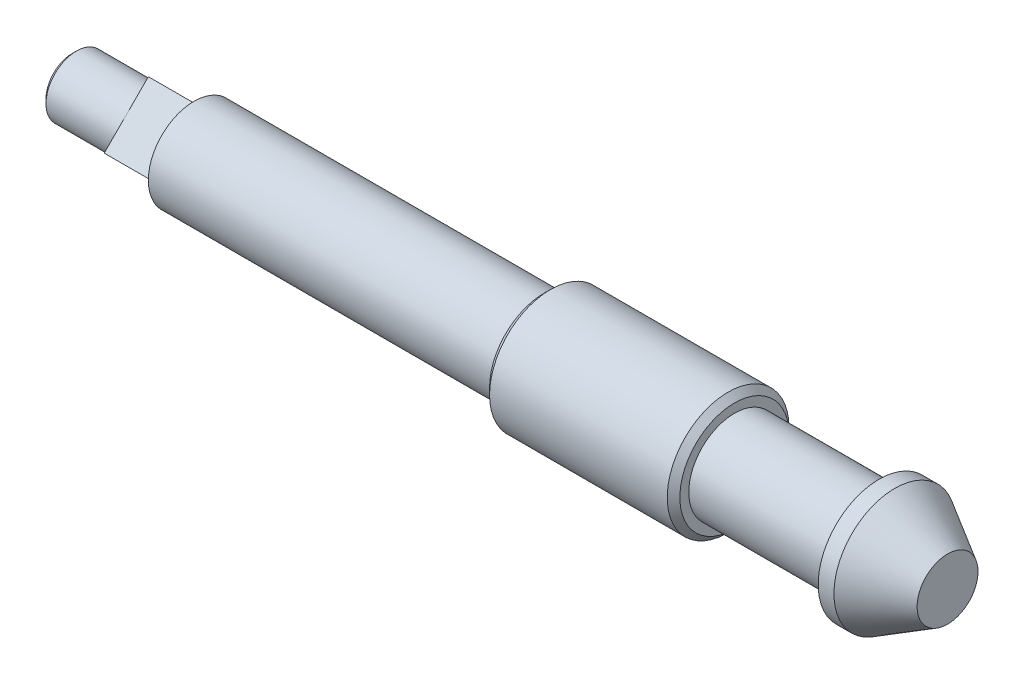
SolidWorks part; units mm, degrees
material "Сталь"
ref_plane "Спереди" through (0, 0, 0) normal (0, 0, 1) x (1, 0, 0)
ref_plane "Сверху" through (0, 0, 0) normal (0, 1, 0) x (1, 0, 0)
ref_plane "Справа" through (0, 0, 0) normal (1, 0, 0) x (0, 0, -1)
sketch "Эскиз1" plane through (0, 0, 0) normal (0, 0, 1) x (1, 0, 0)
  line L0 (0, 0) -> (-155.4845, 0) construction
  line L1 (0, 0) -> (0, 4)
  line L2 (0, 4) -> (-6.9282, 8)
  line L3 (-6.9282, 8) -> (-9, 8)
  line L4 (-9, 8) -> (-9, 6)
  line L5 (-9, 6) -> (-28, 6)
  line L6 (-28, 6) -> (-28, 8)
  line L7 (-28, 8) -> (-53, 8)
  line L8 (-53, 8) -> (-53, 6)
  line L9 (-53, 6) -> (-115, 6)
  line L10 (-115, 6) -> (-115, 0)
  line L11 (0, 0) -> (-115, 0)
  dimension "D1" = 115
  dimension "D2" = 9
  dimension "D3" = 8
  dimension "D4" = 60
  dimension "D5" = 4
  dimension "D6" = 12
  dimension "D7" = 16
  dimension "D8" = 25
  dimension "D9" = 28
revolve "Повернуть1" add sketch "Эскиз1" angle 360 about L0
cosmetic thread "Условное изображение резьбы1" parameters "D1"=5, "D2"=14.344
chamfer "Фаска1" distance 0.828 angle 45 2 edges at (-53, 0, -8) (-28, 0, -8)
sketch "Эскиз2" plane through (-115, 0, 0) normal (-1, 0, 0) x (0, 0, 1)
  circle A0 centre (0, 0) radius 4
  circle A1 centre (0, 0) radius 6 construction
  circle A2 centre (0, 0) radius 6
  dimension "D1" = 8
extrude "Вырез-Вытянуть1" cut sketch "Эскиз2" against normal blind 10
cosmetic thread "Условное изображение резьбы2" parameters "D2"=6.891
sketch "Эскиз3" plane through (-105, 0, 0) normal (-1, 0, 0) x (0, 0, 1)
  line L1 (0, 5.7983) -> (-5.7983, 0)
  line L2 (-5.7983, 0) -> (0, -5.7983)
  line L3 (0, -5.7983) -> (5.7983, 0)
  line L4 (5.7983, 0) -> (0, 5.7983)
  circle A0 centre (0, 0) radius 4.1 construction
  circle A1 centre (0, 0) radius 6
  circle A2 centre (0, 0) radius 6
  dimension "D2" = 8.2
  dimension "D1" = 0
extrude "Вырез-Вытянуть2" cut sketch "Эскиз3" against normal blind 6
chamfer "Фаска2" distance 0.5545 angle 45 1 edges at (-115, 0, 4)
